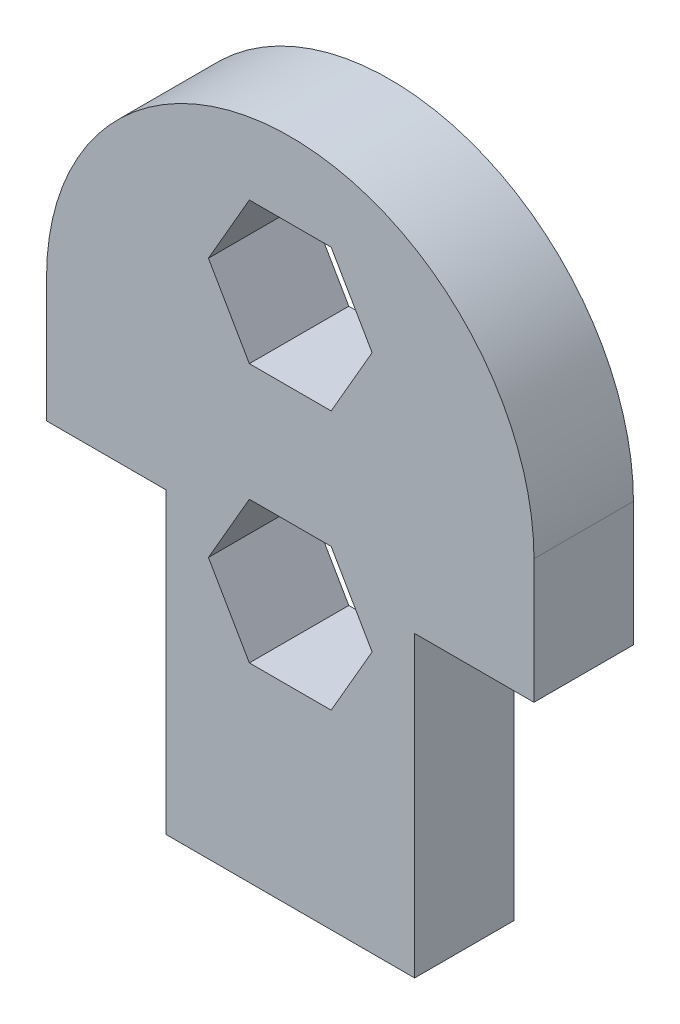
SolidWorks part; units mm, degrees
ref_plane "Front Plane" through (0, 0, 0) normal (0, 0, 1) x (1, 0, 0)
ref_plane "Top Plane" through (0, 0, 0) normal (0, 1, 0) x (1, 0, 0)
ref_plane "Right Plane" through (0, 0, 0) normal (1, 0, 0) x (0, 0, -1)
sketch "Sketch1" plane through (0, 0, 0) normal (0, 0, 1) x (1, 0, 0)
  line L0 (0, 0) -> (10, 0)
  line L1 (0, 0) -> (0, 4)
  line L2 (0, 4) -> (-2.5, 4)
  line L3 (3.3546, 18.0712) -> (6.6454, 18.0712)
  line L4 (-2.5, 4) -> (-2.5, 8)
  line L5 (-2.5, 8) -> (0, 8)
  line L6 (0, 8) -> (0, 12)
  line L7 (5, 0) -> (5, 27) construction
  line L8 (10, 0) -> (10, 4)
  line L9 (10, 4) -> (12.5, 4)
  line L10 (12.5, 4) -> (12.5, 8)
  line L11 (12.5, 8) -> (10, 8)
  line L12 (3.3546, 23.7712) -> (1.7091, 20.9212)
  line L13 (8.2909, 10.5) -> (6.6454, 13.35)
  line L14 (6.6454, 13.35) -> (3.3546, 13.35)
  line L15 (3.3546, 13.35) -> (1.7091, 10.5)
  line L16 (1.7091, 10.5) -> (3.3546, 7.65)
  line L17 (3.3546, 7.65) -> (6.6454, 7.65)
  line L18 (6.6454, 7.65) -> (8.2909, 10.5)
  line L19 (1.7091, 20.9212) -> (3.3546, 18.0712)
  line L20 (0, 12) -> (-4.8, 12)
  line L21 (10, 8) -> (10, 12)
  line L22 (6.6454, 18.0712) -> (8.2909, 20.9212)
  line L23 (8.2909, 20.9212) -> (6.6454, 23.7712)
  line L24 (6.6454, 23.7712) -> (3.3546, 23.7712)
  line L25 (10, 12) -> (14.8, 12)
  line L26 (-4.8, 12) -> (-4.8, 17)
  line L27 (14.8, 12) -> (14.8, 17)
  arc A1 (14.8, 17) -> (-4.8, 17) centre (5, 17) ccw
  dimension "D5" = 2.5
  dimension "D2" = 5.7
  dimension "D8" = 4.8
  dimension "D9" = 4
  dimension "D10" = 4
  dimension "D12" = 2.5
extrude "Boss-Extrude1" add sketch "Sketch1" along normal blind 4
sketch "Sketch2" plane through (0, 0, 4) normal (0, 0, 1) x (1, 0, 0)
  line L0 (-2.5, 8) -> (0, 8)
  line L1 (0, 8) -> (0, 4)
  line L2 (0, 4) -> (-2.5, 4)
  line L3 (-2.5, 4) -> (-2.5, 8)
  line L4 (10, 8) -> (12.5, 8)
  line L5 (12.5, 8) -> (12.5, 4)
  line L6 (12.5, 4) -> (10, 4)
  line L7 (10, 4) -> (10, 8)
extrude "Cut-Extrude1" cut sketch "Sketch2" against normal up to surface (4 mm away) up to face at (5, 20.9212, 0)
equation "\"D8@Sketch1\"= 5 - \"tol2@parametersSketch@prostheticParameters.SLDPRT\""
